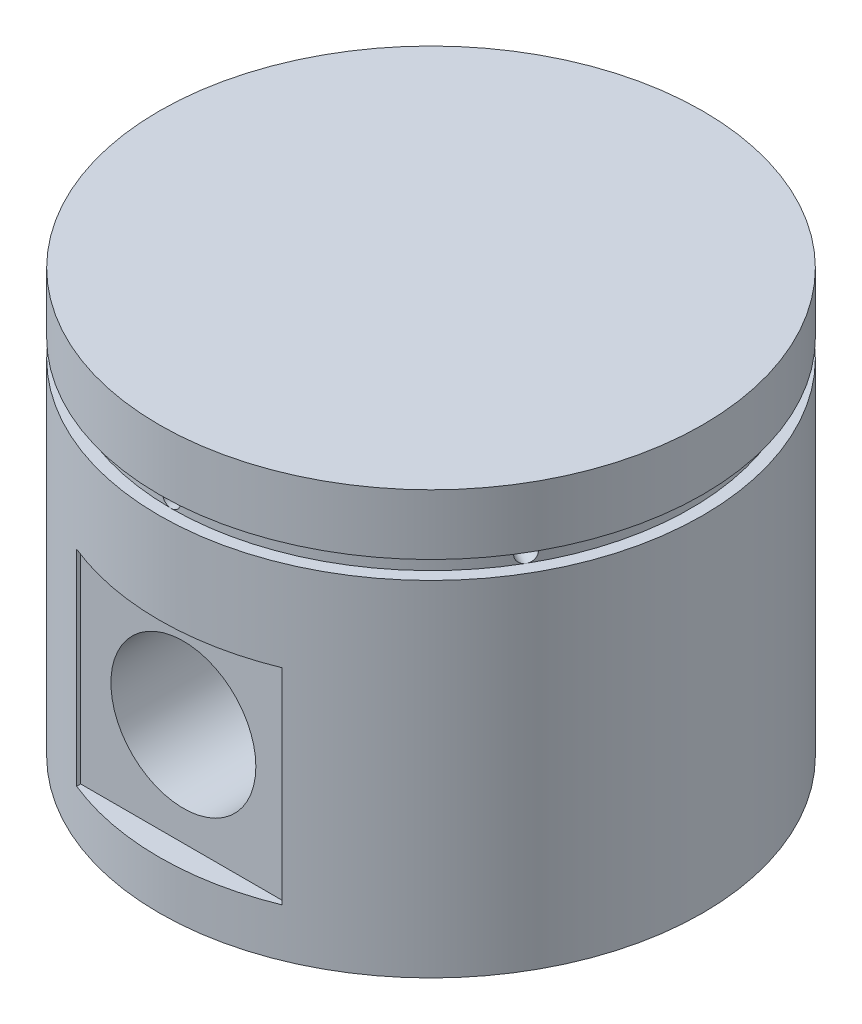
SolidWorks part; units mm, degrees
material "Gri Dökme Demir"
ref_plane "Ön Düzlem" through (0, 0, 0) normal (0, 0, 1) x (1, 0, 0)
ref_plane "Üst Düzlem" through (0, 0, 0) normal (0, 1, 0) x (1, 0, 0)
ref_plane "Sağ Düzlem" through (0, 0, 0) normal (1, 0, 0) x (0, 0, -1)
sketch "Çizim1" plane through (0, 0, 0) normal (0, 1, 0) x (1, 0, 0)
  circle A0 centre (0, 0) radius 45
  dimension "D1" = 90
extrude "Yükseklik-Ekstrüzyon1" add sketch "Çizim1" along normal mid plane 70
ref_plane "Düzlem1" through (0, 0, 45) normal (0, 0, 1) x (1, 0, 0)
sketch "Çizim2" plane through (0, 0, 45) normal (0, 0, 1) x (1, 0, 0)
  line L10 (45, 35) -> (-45, 35) construction
  line L11 (-17, 7) -> (17, 7)
  line L12 (-17, 7) -> (-17, -27)
  line L13 (-17, -27) -> (17, -27)
  line L14 (17, 7) -> (17, -27)
  line L15 (-17, 7) -> (17, -27) construction
  line L16 (-17, -27) -> (17, 7) construction
  point P0 (0, -10)
  dimension "D1" = 45
  dimension "D2" = 34
  dimension "D3" = 34
  dimension "D4" = 10
extrude "Kes-Ekstrüzyon1" cut sketch "Çizim2" against normal blind 4
mirror "Aynalama1" about plane through (0, 0, 0) normal (0, 0, 1) of "Kes-Ekstrüzyon1"
sketch "Çizim5" plane through (0, 0, 45) normal (0, 0, 1) x (1, 0, 0)
  circle A0 centre (0, -10) radius 12
  dimension "D1" = 24
extrude "Kes-Ekstrüzyon2" cut sketch "Çizim5" against normal through all
sketch "Çizim7" plane through (0, 0, 0) normal (1, 0, 0) x (0, 0, -1)
  line L0 (45, -35) -> (38, -35)
  line L1 (-45, -35) -> (45, -35) construction
  line L2 (38, -35) -> (38, -27)
  line L3 (0, 0) -> (0, -35) construction
  line L4 (-45, -35) -> (-38, -35)
  line L5 (-38, -35) -> (-38, -27)
  line L6 (-38, -27) -> (38, -27)
  line L7 (12, 11) -> (38, 11)
  line L8 (38, 11) -> (38, 26)
  line L9 (-36, 28) -> (36, 28)
  line L10 (-12, -27) -> (-12, 11)
  line L11 (12, -27) -> (12, 11)
  line L12 (-12, 11) -> (-38, 11)
  line L13 (-38, 11) -> (-38, 26)
  line L14 (-38, -35) -> (38, -35)
  arc A0 (38, 26) -> (36, 28) centre (36, 26) ccw
  arc A1 (-36, 28) -> (-38, 26) centre (-36, 26) ccw
  point P16 (38, 28)
  point P22 (0, -17.5)
  point P26 (-38, 28)
  dimension "D9" = 2
  dimension "D1" = 7
  dimension "D2" = 8
  dimension "D3" = 17
  dimension "D4" = 38
  dimension "D5" = 38
  dimension "D6" = 12
  dimension "D7" = 12
  dimension "D8" = 26
extrude "Kes-Ekstrüzyon3" cut sketch "Çizim7" against normal mid plane 38
ref_plane "Düzlem2" through (0, 23.5, 0) normal (0, 1, 0) x (1, 0, 0)
sketch "Çizim8" plane through (0, 23.5, 0) normal (0, 1, 0) x (1, 0, 0)
  circle A0 centre (0, 0) radius 43
  circle A1 centre (0, 0) radius 45 construction
  circle A2 centre (0, 0) radius 45
  dimension "D1" = 86
extrude "Kes-Ekstrüzyon4" cut sketch "Çizim8" against normal mid plane 3
sketch "Çizim9" plane through (0, 0, 45) normal (0, 0, 1) x (1, 0, 0)
  line L0 (0, 0) -> (0, 25) construction
  line L1 (-43, 25) -> (43, 25) construction
  line L2 (45, 22) -> (-45, 22) construction
  circle A0 centre (0, 23.5) radius 1.5
  point P9 (0, 23.5)
  dimension "D1" = 3
extrude "Kes-Ekstrüzyon5" cut sketch "Çizim9" against normal up to next
pattern_circular "Dairesel Kaplama1" count 6 over 360 about axis through (0, 25, 0) along (0, 1, 0) of "Kes-Ekstrüzyon5"
